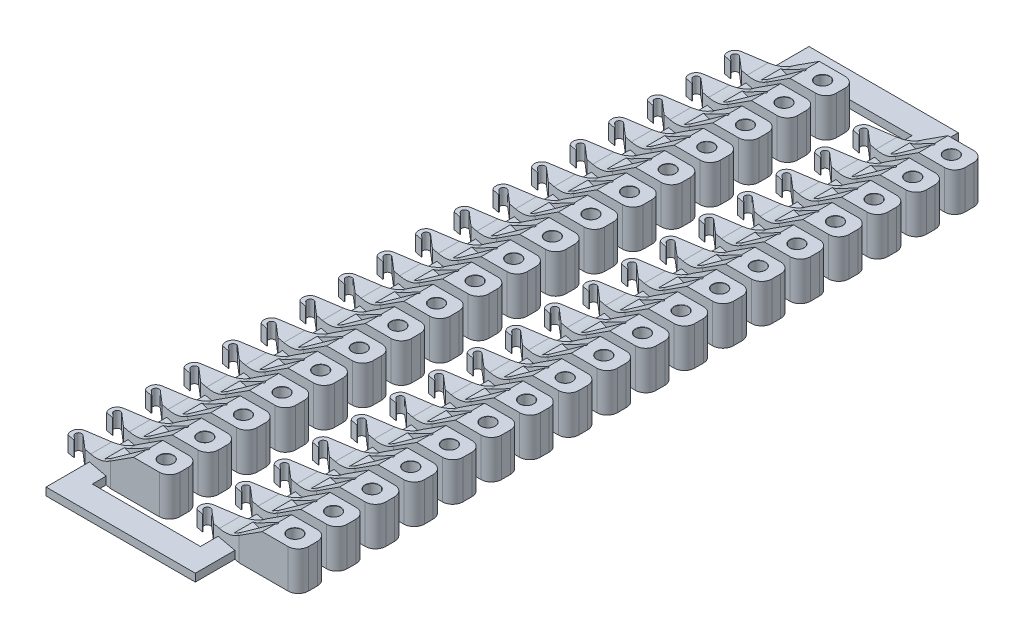
SolidWorks part; units mm, degrees
ref_plane "Front Plane" through (0, 0, 0) normal (0, 0, 1) x (1, 0, 0)
ref_plane "Top Plane" through (0, 0, 0) normal (0, 1, 0) x (1, 0, 0)
ref_plane "Right Plane" through (0, 0, 0) normal (1, 0, 0) x (0, 0, -1)
sketch "Sketch1" plane through (0, 0, 0) normal (0, 1, 0) x (1, 0, 0)
  line L0 (0.7, 0.57) -> (-1.6, 0.57)
  line L1 (0.7, 0.57) -> (0.7, -0.57)
  line L2 (0.7, -0.57) -> (-1.6, -0.57)
  line L3 (-1.6, 0.57) -> (-3.681, 0.25)
  line L4 (-3.4049, 0) -> (-2.2666, -0.982) construction
  line L5 (-1.6, -0.57) -> (-3.7439, -0.166)
  line L6 (0, 0) -> (-4.3932, 0) construction
  line L7 (-3.3232, 0.0948) -> (-2.1848, -0.8872)
  line L8 (-3.4867, -0.0948) -> (-2.3484, -1.0768)
  line L9 (-3.341, 0) -> (-3.341, -0.5283)
  line L13 (1.2, 1.1) -> (1.2, -1.1)
  circle A0 centre (0, 0) radius 0.27
  circle A1 centre (-3.7, 0) radius 0.1717
  arc A2 (-3.3232, 0.0948) -> (-3.4867, -0.0948) centre (-3.4049, 0) ccw
  arc A3 (-2.3484, -1.0768) -> (-2.1848, -0.8872) centre (-2.2666, -0.982) ccw
  circle A4 centre (-3.4049, 0) radius 0.2891
  point P13 (-2.8358, -0.491)
  dimension "D1" = 0.57
  dimension "D9" = 0.54
  dimension "D2" = 0.57
  dimension "D3" = 0.7
  dimension "D4" = 1.6
  dimension "D5" = 1.6
  dimension "D6" = 0.25
  dimension "D12" = 0.5
extrude "Boss-Extrude1" add sketch "Sketch1" along normal blind 1.5
pattern_linear "LPattern1" [suppressed] count 9 spacing 3.2 count 4 spacing 6.2
sketch "Sketch2" plane through (0, 0, 0) normal (0, 0, 1) x (1, 0, 0)
  line L0 (-4.2545, 0.6) -> (-2.1, 0.6)
  line L1 (-2.1, 0.6) -> (-0.7, 1.5)
  line L2 (-0.7, 1.5) -> (-4.2545, 1.5)
  line L3 (-4.2545, 1.5) -> (-4.2545, 0.6)
  line L4 (0.7, 1.5) -> (0.7, 0) construction
  line L5 (-1.6, 0) -> (-2.8188, 0) construction
  dimension "D1" = 0.6
  dimension "D2" = 1.4
  dimension "D3" = 2.8
extrude "Cut-Extrude1" cut sketch "Sketch2" against normal through all and the other way through all
fillet "Fillet1" radius 0.01 2 edges at (0, 1.5, 0.27) (0, 0, 0.27)
fillet "Fillet2" radius 1.5 1 edges at (-2.1, 0.6, -0.0087)
fillet "Fillet3" radius 0.4 2 edges at (0.7, 0.75, -0.57) (0.7, 0.75, 0.57)
sketch "Sketch4" plane through (0, 1.5, 0) normal (0, 1, 0) x (1, 0, 0)
  line L0 (-0.5, 0) -> (-2.5, 0.5)
  line L2 (-2.5, 0.5) -> (-2.5, -0.5)
  line L3 (-2.5, -0.5) -> (-0.5, 0)
  dimension "D1" = 0.5
  dimension "D2" = 0.5
  dimension "D3" = 0.5
  dimension "D4" = 2.5
extrude "Cut-Extrude2" cut sketch "Sketch4" against normal blind 0.8
fillet "Fillet4" radius 0.05 1 edges at (-0.5, 1.1, 0)
pattern_linear "LPattern2" count 18 spacing 1.5 along (0, 0, -1) of bodies 134 103
sketch "Sketch3" plane through (0, 0, 0) normal (0, 0, 1) x (1, 0, 0)
  line L1 (-2.6, 0.3) -> (-1.8, 0.3)
  line L2 (-2.6, 0.3) -> (-2.6, 0)
  line L3 (-2.6, 0) -> (-1.8, 0)
  line L4 (-1.8, 0.3) -> (-1.8, 0)
  dimension "D1" = 0.3
  dimension "D3" = 0.8
  dimension "D4" = 1.8
extrude "Boss-Extrude2" add sketch "Sketch3" against normal blind 27 and the other way blind 2.0001
pattern_linear "LPattern4" count 2 spacing 5 along (-1, 0, 0) of bodies 109
sketch "Sketch5" plane through (0, 0, 0) normal (0, 1, 0) x (1, 0, 0)
  line L0 (-7.6, -2.0001) -> (-7.6, -0.3816) construction
  line L1 (-7.6, -1.07) -> (-1.8, -1.07)
  line L2 (-7.6, -1.07) -> (-7.6, -2.0001)
  line L3 (-7.6, -2.0001) -> (-1.8, -2.0001)
  line L4 (-1.8, -1.07) -> (-1.8, -2.0001)
  line L5 (-7.6, 25.9162) -> (-7.6, 27) construction
  line L6 (-1.8, -2.0001) -> (-7.6, -2.0001)
  line L7 (-1.8, -2.0001) -> (-1.8, -2.07)
  line L8 (-1.8, -2.07) -> (-7.6, -2.07)
  line L9 (-7.6, -2.0001) -> (-7.6, -2.07)
  line L10 (-7.6, 26.57) -> (-1.8, 26.57)
  line L11 (-7.6, 26.57) -> (-7.6, 27)
  line L12 (-7.6, 27) -> (-1.8, 27)
  line L13 (-1.8, 26.57) -> (-1.8, 27)
  line L14 (-4.7, 26.07) -> (-5.7, 26.07) construction
  line L15 (-1.8, 27) -> (-7.6, 27)
  line L16 (-1.8, 27) -> (-1.8, 27.57)
  line L17 (-1.8, 27.57) -> (-7.6, 27.57)
  line L18 (-7.6, 27) -> (-7.6, 27.57)
  line L19 (-4.7, -0.57) -> (-5.7, -0.57) construction
  dimension "D1" = 0.5
  dimension "D2" = 0.5
  dimension "D3" = 1
  dimension "D4" = 1
extrude "Boss-Extrude3" add sketch "Sketch5" along normal blind 0.3 contours L4 L1 L2 L3 | L3 L9 L8 L7 | L10 L13 L12 L11 | L18 L12 L16 L17
